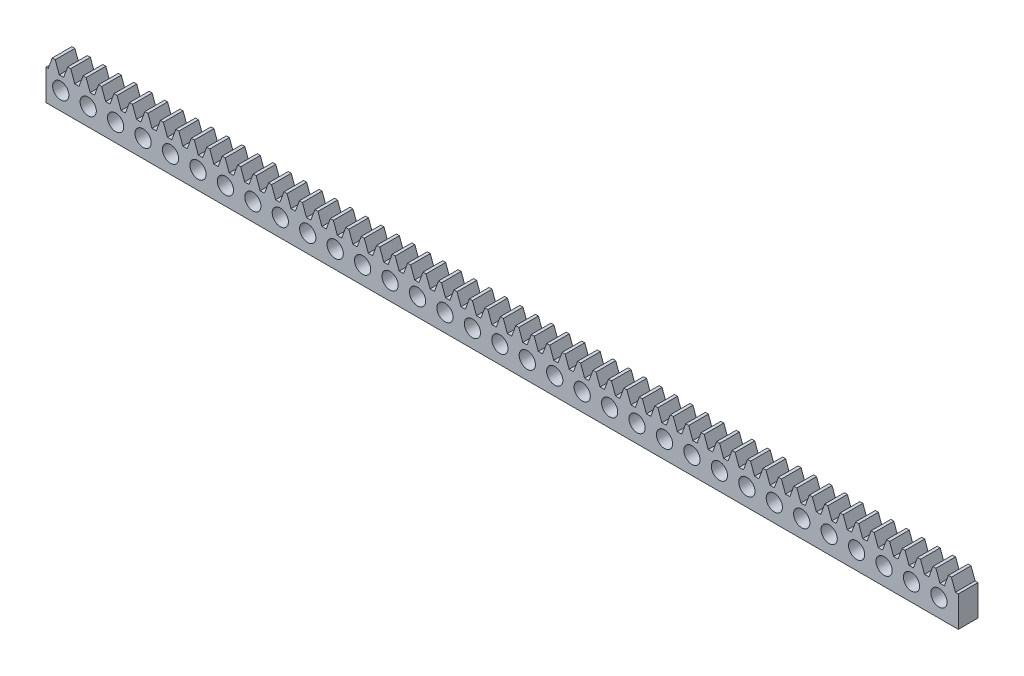
SolidWorks part; units mm, degrees
ref_plane "Plane1" through (0, 0, 0) normal (0, 0, 1) x (1, 0, 0)
ref_plane "Plane2" through (0, 0, 0) normal (0, 1, 0) x (1, 0, 0)
ref_plane "Plane3" through (0, 0, 0) normal (1, 0, 0) x (0, 0, -1)
sketch "HoldingSke" plane through (0, 0, 0) normal (0, 1, 0) x (1, 0, 0)
  line L0 (0, 0) -> (0.1392, 0.9903)
  line L1 (-15, 0) -> (100, 0) construction
  line L2 (0, 0) -> (-2.1039, 2.3779)
  line L3 (0, 0) -> (-11.863, 4.5341)
  line L4 (0, 0) -> (4.1868, 7.5532)
  line L5 (0, 0) -> (-23.7986, -8.8762)
  line L6 (0, 0) -> (-10.5278, -7.1032)
  line L9 (-71.009, 38.7566) -> (103.304, 102.2013)
  line L10 (-76.2, 3.3779) -> (-69.7, 3.3779)
  line L11 (0, 0) -> (-4, 0)
  line L12 (-76.2, 101.6) -> (-76.162, 101.6)
  line L13 (24.9733, 27.94) -> (52.9518, 28.4284)
  line L14 (24.9733, 27.94) -> (24.9743, 27.94)
  line L15 (24.9733, 27.94) -> (100.4006, 29.5858)
  circle A0 centre (0, 0) radius 19.05
  circle A1 centre (0, 0) radius 3.25
  circle A2 centre (0, 0) radius 12.7
  dimension "MPH" = 6.5
  dimension "Diameter" = 38.1
  dimension "Num_teeth" = 61
  dimension "Pitch" = 1
  dimension "Width" = 4
  dimension "Show_teeth" = 998
  dimension "Thickness" = 12.7
  dimension "Ap" = 20
  dimension "Pitch_height" = 6.5
  dimension "Backlash" = 0.038
  dimension "Addendum_fac" = 1
  dimension "Dedendum_fac" = 1.25
  dimension "Clearance_fac" = 0.25
  dimension "Dedendum_add" = 0.001
  dimension "Length" = 185.5
  dimension "Module" = 1
sketch "BlankSke" plane through (0, 0, 0) normal (0, 0, 1) x (1, 0, 0)
  line L1 (0, 0) -> (185.5, 0)
  line L2 (0, 0) -> (0, 7.5)
  line L3 (0, 7.5) -> (185.5, 7.5)
  line L4 (185.5, 0) -> (185.5, 7.5)
  dimension "Length" = 185.5
  dimension "Blank_height" = 7.5
extrude "Blank" add sketch "BlankSke" against normal blind 4
sketch "TooCutSkeIll" plane through (0, 0, 0) normal (0, 0, 1) x (1, 0, 0)
  line L0 (-1.2538, 7.4737) -> (-0.5045, 5.4152)
  line L1 (-0.2687, 5.25) -> (0.2687, 5.25)
  line L2 (0.5045, 5.4152) -> (1.2538, 7.4737)
  line L3 (185.5, 7.5) -> (0, 7.5) construction
  line L4 (0, 0) -> (0, 64.897) construction
  line L5 (-13.208, 6.5) -> (12.954, 6.5) construction
  line L6 (0, 0) -> (185.5, 0) construction
  line L7 (0.8994, 6.5) -> (0.8994, 48.7463) construction
  line L8 (-0.8994, 6.5) -> (-0.8994, 48.7463) construction
  line L9 (1.2914, 7.5) -> (1.2914, 7.5254)
  line L10 (-1.2914, 7.5) -> (-1.2914, 7.5254)
  line L11 (-1.2914, 7.5254) -> (1.2914, 7.5254)
  arc A0 (0.2687, 5.25) -> (0.5045, 5.4152) centre (0.2687, 5.501) ccw
  arc A1 (-0.5045, 5.4152) -> (-0.2687, 5.25) centre (-0.2687, 5.501) ccw
  arc A2 (1.2914, 7.5) -> (1.2538, 7.4737) centre (1.2914, 7.46) ccw
  arc A3 (-1.2538, 7.4737) -> (-1.2914, 7.5) centre (-1.2914, 7.46) ccw
  dimension "Root_fillet" = 0.251
  dimension "Break_rad" = 0.04
  dimension "Pitch_height" = 6.5
  dimension "Gap_width" = 1.7988
  dimension "Dedendum" = 1.25
  dimension "Addendum_plus" = 1.0254
  dimension "Pressure_angle" = 20
extrude "ToothCutIll" [suppressed] cut sketch "TooCutSkeIll" against normal through all
sketch "TooCutSkeSim" plane through (0, 0, 0) normal (0, 0, 1) x (1, 0, 0)
  line L0 (0.4444, 5.25) -> (-0.4444, 5.25)
  line L1 (1.2726, 7.5254) -> (0.4444, 5.25)
  line L2 (0, 17.4625) -> (0, 53.467) construction
  line L3 (1.2726, 7.5254) -> (-1.2726, 7.5254)
  line L6 (-1.2726, 7.5254) -> (-0.4444, 5.25)
  line L9 (-0.8994, 6.5) -> (0.8994, 6.5) construction
  line L10 (0, 0) -> (185.5, 0) construction
  line L11 (0.8994, 6.5) -> (0.8994, 53.467) construction
  line L12 (-0.8994, 6.5) -> (-0.8994, 53.467) construction
  dimension "Pitch_height" = 6.5
  dimension "Pressure_angle" = 20
  dimension "Gap_width" = 1.7988
  dimension "Dedendum" = 1.25
  dimension "Addendum_plus" = 1.0254
extrude "ToothCutSim" cut sketch "TooCutSkeSim" against normal through all
pattern_linear "TeethCuts" count 60 spacing 3.1416 along (1, 0, 0) of "ToothCutIll", "ToothCutSim"
sketch "Skizze1" plane through (0, 0, 0) normal (0, 0, 1) x (1, 0, 0)
  line L0 (0, 2.625) -> (185.5, 2.625) construction
  line L1 (0, 5.25) -> (0, 0) construction
  line L2 (185.5, 0) -> (185.5, 5.25) construction
  circle A0 centre (3, 2.625) radius 1.65
  dimension "D1" = 3.3
  dimension "D2" = 3
extrude "Schnitt-Linear austragen1" cut sketch "Skizze1" against normal blind 10
pattern_linear "Lineares Muster1" count 33 spacing 5.58 along (1, 0, 0) of "Schnitt-Linear austragen1"
sketch "base-line" plane through (0, 0, 0) normal (0, 0, 1) x (1, 0, 0)
  line L0 (185.5, 2.625) -> (185.5, -2.7625) construction
  line L1 (0, 0) -> (185.5, 0)
  line L2 (0, 0) -> (0, -1)
  line L3 (0, -1) -> (185.5, -1)
  line L4 (185.5, 0) -> (185.5, -1)
  line L5 (185.5, 0) -> (185.5, 5.25) construction
  dimension "D1" = 1
extrude "base" add sketch "base-line" against normal blind 4
equation "' \"Module@HoldingSke\" = 6.35"
equation "' \"Num_teeth@HoldingSke\" = 12"
equation "' \"Ap@HoldingSke\" =  20"
equation "' \"Width@HoldingSke\" = 0.25 * 25.4"
equation "' \"Show_teeth@HoldingSke\" = 500"
equation "' \"Backlash@HoldingSke\" = 0.009 * 25.4"
equation "' \"Addendum_fac@HoldingSke\" = 1.0"
equation "' \"Dedendum_fac@HoldingSke\" = 1.25"
equation "' \"Dedendum_add@HoldingSke\" = 0.00005 * 25.4"
equation "' \"Clearance_fac@HoldingSke\" = 0.25"
equation "' \"Pitch_height@HoldingSke\" = 1 * 25.4"
equation "' \"Length@HoldingSke\" = 4.71 * 25.4"
equation "\"Pitch@HoldingSke\" = 1 / \"Module@HoldingSke\""
equation "\"MPH@HoldingSke\" = \"Dedendum_fac@HoldingSke\" / \"Pitch@HoldingSke\" + 2 * \"Dedendum_add@HoldingSke\" + 0.002 * 25.4"
equation "\"MPH@HoldingSke\" = ((sgn( \"MPH@HoldingSke\" - \"Pitch_height@HoldingSke\")+1)*( \"MPH@HoldingSke\" - \"Pitch_height@HoldingSke\"))/2 + \"Pitch_height@HoldingSke\""
equation "\"Blank_height@BlankSke\" = \"Pitch_height@HoldingSke\" + \"Addendum_fac@HoldingSke\"  / \"Pitch@HoldingSke\" "
equation "\"Length@BlankSke\" =  \"Length@HoldingSke\""
equation "\"Face_width@Blank\" = \"Width@HoldingSke\""
equation "\"Pressure_angle@TooCutSkeIll\" = \"Ap@HoldingSke\""
equation "\"Addendum_plus@TooCutSkeIll\" =  \"Addendum_fac@HoldingSke\"  / \"Pitch@HoldingSke\" + 0.001 *25.4"
equation "\"Dedendum@TooCutSkeIll\" = \"Dedendum_fac@HoldingSke\"  / \"Pitch@HoldingSke\""
equation "\"Pitch_height@TooCutSkeIll\" =  \"MPH@HoldingSke\""
equation "\"Gap_width@TooCutSkeIll\" = 3.14159265 / 2 / \"Pitch@HoldingSke\" + 6 * \"Backlash@HoldingSke\""
equation "\"Pressure_angle@TooCutSkeSim\" = \"Ap@HoldingSke\""
equation "\"Addendum_plus@TooCutSkeSim\" =  \"Addendum_fac@HoldingSke\"  / \"Pitch@HoldingSke\" + 0.001 * 25.4"
equation "\"Dedendum@TooCutSkeSim\" = \"Dedendum_fac@HoldingSke\"  / \"Pitch@HoldingSke\""
equation "\"Pitch_height@TooCutSkeSim\" =  \"MPH@HoldingSke\""
equation "\"Gap_width@TooCutSkeSim\" = 3.14159265 / 2 / \"Pitch@HoldingSke\" + 6 * \"Backlash@HoldingSke\""
equation "\"Root_fillet@TooCutSkeIll\" = \"Clearance_fac@HoldingSke\" / \"Pitch@HoldingSke\" + \"Dedendum_add@HoldingSke\""
equation "\"Break_rad@TooCutSkeIll\" = 0.02 / \"Pitch@HoldingSke\" * 2"
equation "\"Linear_pitch@TeethCuts\" = 3.14159265 / \"Pitch@HoldingSke\""
equation "\"Num_teeth@HoldingSke\" = int( ( \"Length@HoldingSke\" + 0 ) / (3.14159265 / \"Pitch@HoldingSke\")) + 0.9999  + 1"
equation " \"Num_teeth@TeethCuts\" = int( \"Show_teeth@HoldingSke\" ) + 1"
equation " \"Num_teeth@TeethCuts\" = ((sgn( \"Num_teeth@TeethCuts\" - \"Num_teeth@HoldingSke\" )-1)*( \"Num_teeth@TeethCuts\" - \"Num_teeth@HoldingSke\" ))/-2+ \"Num_teeth@HoldingSke\""
equation " \"Num_teeth@TeethCuts\" = ((sgn( \"Num_teeth@TeethCuts\" - 2.0)+1)*( \"Num_teeth@TeethCuts\" - 2.0))/2 +2.0"
